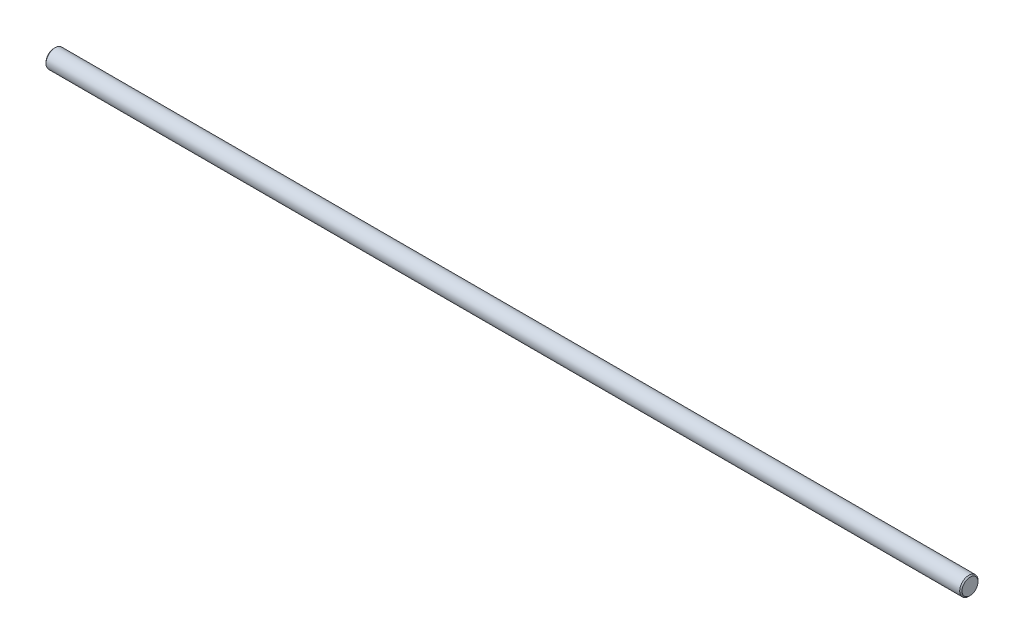
SolidWorks part; units mm, degrees
ref_plane "Front Plane" through (0, 0, 0) normal (0, 0, 1) x (1, 0, 0)
ref_plane "Top Plane" through (0, 0, 0) normal (0, 1, 0) x (1, 0, 0)
ref_plane "Right Plane" through (0, 0, 0) normal (1, 0, 0) x (0, 0, -1)
ref_plane "Plane1" through (0, 0, 0) normal (0, 0, 1) x (1, 0, 0)
sketch "Sketch1" plane through (0, 0, 0) normal (0, 0, 1) x (1, 0, 0)
  line L0 (0, 0) -> (0, 3.5)
  line L1 (0, 3.5) -> (0.5, 4)
  line L2 (0.5, 4) -> (399.5, 4)
  line L3 (399.5, 4) -> (400, 3.5)
  line L4 (400, 3.5) -> (400, 0)
  line L5 (400, 0) -> (0, 0)
  line L6 (400, 0) -> (0, 0) construction
revolve "Revolve1" add sketch "Sketch1" angle 360 about L6
ref_plane "Plane2" through (200, 0, 0) normal (-1, 0, 0) x (0, 0, 1)
